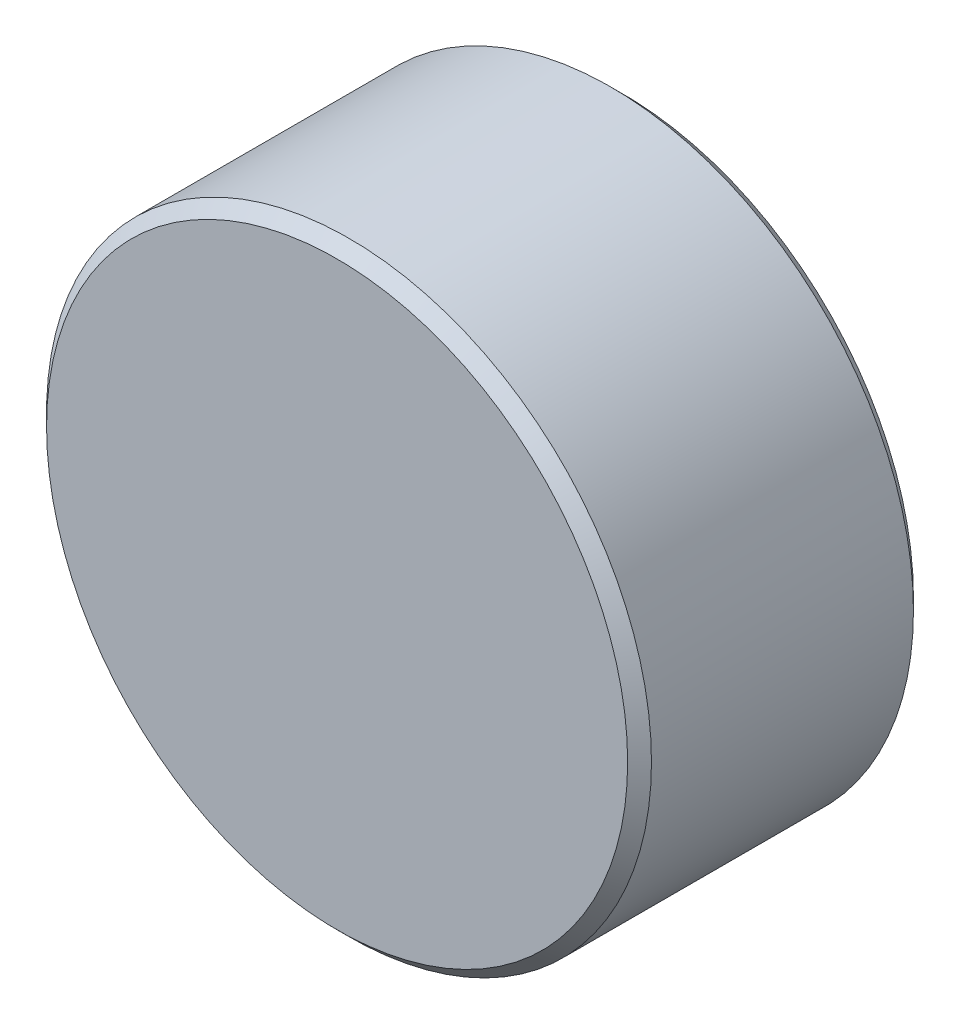
SolidWorks part; units mm, degrees
ref_plane "Front Plane" through (0, 0, 0) normal (0, 0, 1) x (1, 0, 0)
ref_plane "Top Plane" through (0, 0, 0) normal (0, 1, 0) x (1, 0, 0)
ref_plane "Right Plane" through (0, 0, 0) normal (1, 0, 0) x (0, 0, -1)
sketch "Sketch18" plane through (0, 0, 0) normal (0, 0, 1) x (1, 0, 0)
  circle A0 centre (0, 0) radius 6.35
  dimension "D1" = 12.7
extrude "Boss-Extrude2" add sketch "Sketch18" along normal mid plane 6
chamfer "Chamfer4" distance 0.25 angle 45 2 edges at (6.35, 0, -3) (6.35, 0, 3)
